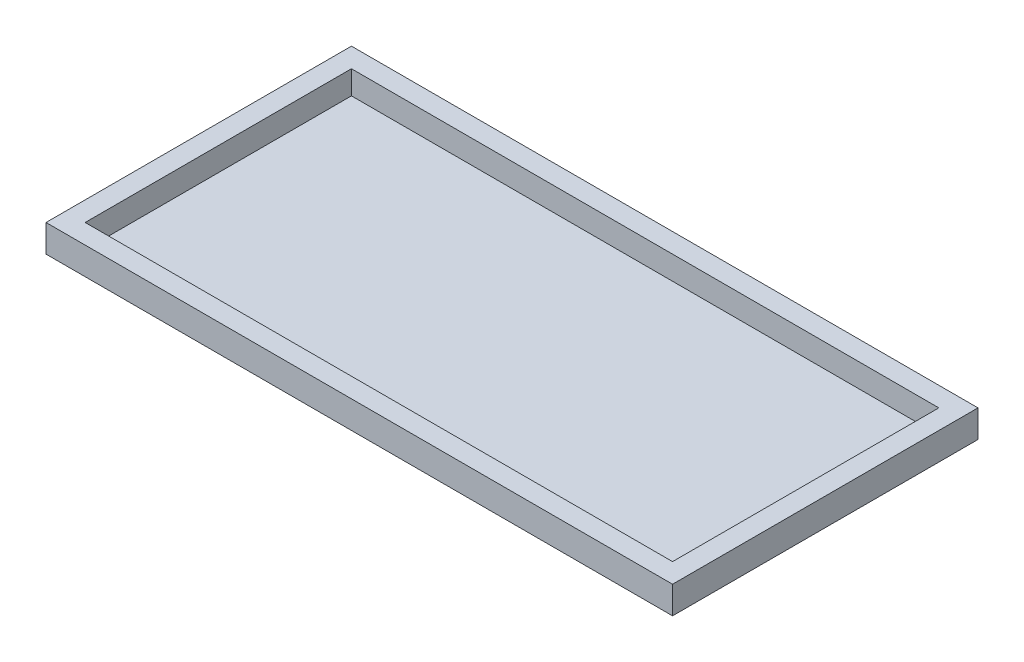
SolidWorks part; units mm, degrees
ref_plane "Alzado" through (0, 0, 0) normal (0, 0, 1) x (1, 0, 0)
ref_plane "Planta" through (0, 0, 0) normal (0, 1, 0) x (1, 0, 0)
ref_plane "Vista lateral" through (0, 0, 0) normal (1, 0, 0) x (0, 0, -1)
sketch "Croquis1" plane through (0, 0, 0) normal (0, 1, 0) x (1, 0, 0)
  line L1 (-75, -34) -> (75, -34)
  line L2 (-75, -34) -> (-75, 34)
  line L3 (-75, 34) -> (75, 34)
  line L4 (75, -34) -> (75, 34)
  line L5 (-75, -34) -> (75, 34) construction
  line L6 (-75, 34) -> (75, -34) construction
  line L7 (-80, -39) -> (80, -39)
  line L8 (-80, -39) -> (-80, 39)
  line L9 (-80, 39) -> (80, 39)
  line L10 (80, -39) -> (80, 39)
  line L11 (-80, -39) -> (80, 39) construction
  line L12 (-80, 39) -> (80, -39) construction
  point P0 (0, 0)
  point P6 (0, 0)
  dimension "D1" = 68
  dimension "D2" = 150
  dimension "D3" = 78
  dimension "D4" = 160
extrude "Saliente-Extruir1" add sketch "Croquis1" along normal blind 6
sketch "Croquis2" plane through (0, 0, 0) normal (0, -1, 0) x (1, 0, 0)
  line L1 (-80, -39) -> (80, -39)
  line L2 (-80, -39) -> (-80, 39)
  line L3 (-80, 39) -> (80, 39)
  line L4 (80, -39) -> (80, 39)
  line L5 (-80, -39) -> (80, 39) construction
  line L6 (-80, 39) -> (80, -39) construction
  point P0 (0, 0)
extrude "Saliente-Extruir2" add sketch "Croquis2" along normal blind 1
